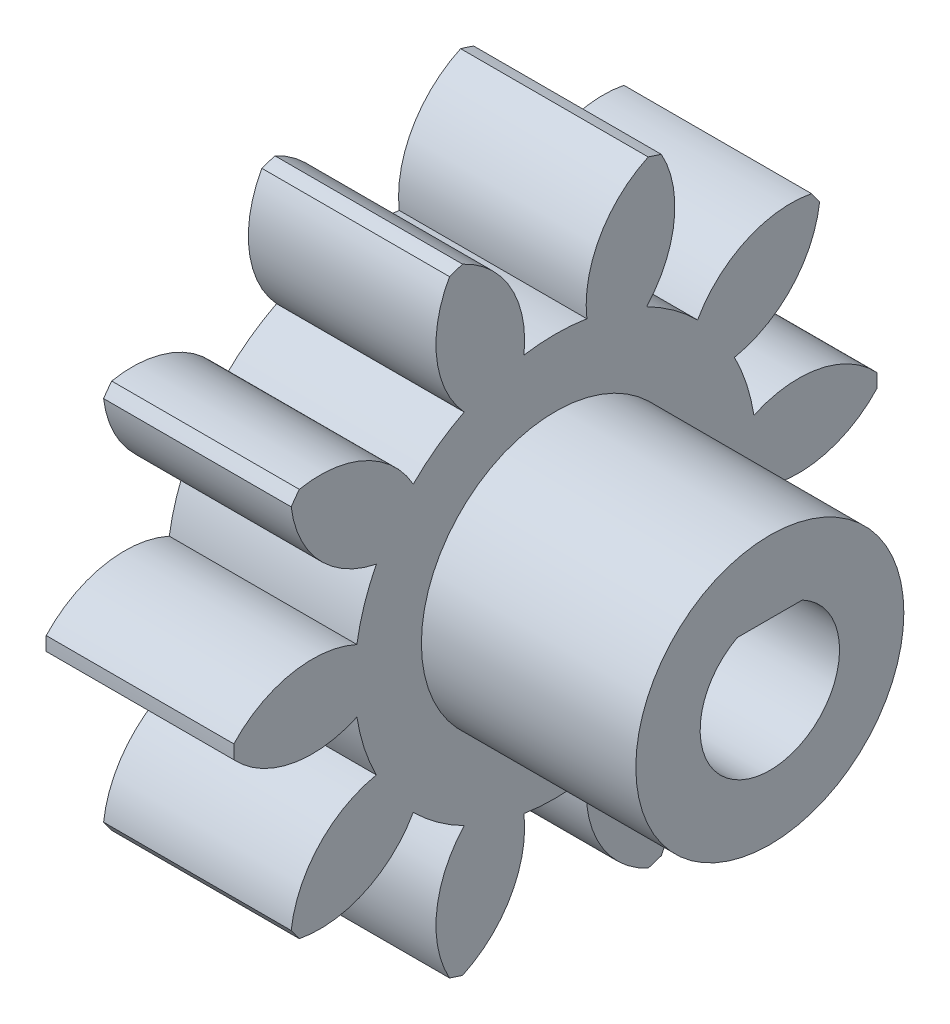
SolidWorks part; units mm, degrees
ref_plane "Plane1" through (0, 0, 0) normal (0, 0, 1) x (1, 0, 0)
ref_plane "Plane2" through (0, 0, 0) normal (0, 1, 0) x (1, 0, 0)
ref_plane "Plane3" through (0, 0, 0) normal (1, 0, 0) x (0, 0, -1)
other "Configuration Table"
sketch "HoldingSke" plane through (0, 0, 0) normal (0, 1, 0) x (1, 0, 0)
  line L0 (0, 0) -> (0.4924, -0.0868)
  line L1 (-15, 0) -> (100, 0) construction
  line L2 (0, 0) -> (-2.1039, 2.3779)
  line L3 (0, 0) -> (-11.863, 4.5341)
  line L4 (0, 0) -> (8.5048, 1.4996)
  line L5 (0, 0) -> (-46.8476, -17.4728)
  line L6 (0, 0) -> (-12.4344, -8.3896)
  line L7 (-2.1039, 2.3779) -> (8.6586, 51.2059)
  line L8 (-76.2, 54.61) -> (-76.1, 54.61)
  line L9 (-71.009, 38.7566) -> (-53.1078, 45.2721)
  line L10 (-76.2, 71.12) -> (104.1128, 71.12)
  line L11 (0, 0) -> (-15, 0)
  line L12 (-76.2, 101.6) -> (-76.133, 101.6)
  line L13 (24.9733, 27.94) -> (52.9518, 28.4284)
  line L14 (24.9733, 27.94) -> (24.9743, 27.94)
  line L15 (24.9733, 27.94) -> (100.4006, 29.5858)
  line L16 (-63.627, -2) -> (-12.827, -2)
  circle A0 centre (0, 0) radius 0.45
  circle A1 centre (0, 0) radius 7.499
  circle A2 centre (0, 0) radius 37.5
  circle A3 centre (0, 0) radius 0.45
  dimension "MHD" = 14.998
  dimension "Hub_dia" = 75
  dimension "Bore" = 0.9
  dimension "MBD" = 0.9
  dimension "Num_teeth" = 10
  dimension "Pitch" = 0.5
  dimension "Overall_len" = 50
  dimension "Show_teeth" = 10
  dimension "Thickness" = 15
  dimension "OAL" = 50.0001
  dimension "T_dim" = 0.1
  dimension "Ap" = 20
  dimension "H" = 19.05
  dimension "Pitch_radius" = 180.3128
  dimension "Width" = 15
  dimension "Backlash" = 0.067
  dimension "Addendum_fac" = 1
  dimension "Dedendum_fac" = 1.25
  dimension "Clearance_fac" = 0.25
  dimension "Dedendum_add" = 0.001
  dimension "Module" = 2
sketch "BasProSke" plane through (0, 0, 0) normal (0, 1, 0) x (1, 0, 0)
  line L0 (-10, 0) -> (60, 0) construction
  line L1 (0, 0) -> (0, 12)
  line L2 (0, 0) -> (15, 0)
  line L3 (15, 0) -> (15, 12)
  line L4 (15, 12) -> (0, 12)
  dimension "Thickness" = 15
  dimension "Diameter" = 24
revolve "Base-Revolve" add sketch "BasProSke" angle 360 about L0
sketch "TooCutSke" plane through (0, 0, 0) normal (1, 0, 0) x (0, 0, -1)
  line L1 (0, 0) -> (0, 107) construction
  line L2 (0, 0) -> (-1.6814, 9.8576) construction
  line L3 (0, 0) -> (-6.1153, 18.8209) construction
  line L4 (-1.6814, 9.8576) -> (-3.0576, 9.4105) construction
  arc A0 (1.1737, 7.4066) -> (-1.1737, 7.4066) centre (0, 0) ccw
  arc A1 (3.4979, 11.5054) -> (-3.4979, 11.5054) centre (0, 0) ccw
  circle A2 centre (0, 0) radius 10 construction
  circle A3 centre (0, 0) radius 9.3969 construction
  arc A4 (-1.1737, 7.4066) -> (-3.4979, 11.5054) centre (-5.1477, 7.8615) ccw
  arc A5 (3.4979, 11.5054) -> (1.1737, 7.4066) centre (5.1477, 7.8615) ccw
  dimension "Root_dia" = 14.998
  dimension "Overcut_dia" = 24.0508
  dimension "Pitch_dia" = 20
  dimension "Base_dia" = 18.7939
  dimension "Flank_rad" = 4
  dimension "Half_ang" = 18
  dimension "Half_CT" = 1.4471
extrude "ToothCut" cut sketch "TooCutSke" along normal through all
fillet "Breaks" [suppressed] radius 0.04
fillet "RootFillets" [suppressed] radius 0.501
pattern_circular "TeethCuts" count 10 every 36 about axis through (-10, 0, 0) along (1, 0, 0) of "ToothCut", "RootFillets", "Breaks"
sketch "HubNeaOneSke" plane through (0, 0, 0) normal (-1, 0, 0) x (0, 0, 1)
  circle A0 centre (0, 0) radius 7.499
  dimension "Diameter" = 14.998
extrude "HubNearOne" [suppressed] add sketch "HubNeaOneSke" along normal blind 35.0001
sketch "HubNeaBotSke" plane through (0, 0, 0) normal (-1, 0, 0) x (0, 0, 1)
  circle A0 centre (0, 0) radius 7.499
  dimension "Diameter" = 14.998
extrude "HubNearBoth" [suppressed] add sketch "HubNeaBotSke" along normal blind 17.5
ref_plane "FarPln" through (15, 0, 0) normal (1, 0, 0) x (0, 0, -1)
sketch "HubFarSke" plane through (15, 0, 0) normal (1, 0, 0) x (0, 0, -1)
  circle A0 centre (0, 0) radius 7.499
  dimension "Diameter" = 14.998
extrude "HubFar" [suppressed] add sketch "HubFarSke" along normal blind 17.5
sketch "BorSke" plane through (0, 0, 0) normal (1, 0, 0) x (0, 0, -1)
  circle A0 centre (0, 0) radius 0.45
  dimension "Diameter" = 0.9
extrude "Bore" cut sketch "BorSke" along normal mid plane 100.0001
sketch "KeySke" plane through (0, 0, 0) normal (1, 0, 0) x (0, 0, -1)
  line L0 (-0.05, 0) -> (-0.05, 0.55)
  line L1 (-0.05, 0.55) -> (0.05, 0.55)
  line L2 (0.05, 0.55) -> (0.05, 0)
  line L3 (0, 0) -> (0, 34) construction
  line L4 (-0.05, 0) -> (0.05, 0)
  dimension "Offset" = 0.55
  dimension "Width" = 0.1
extrude "Keyway" [suppressed] cut sketch "KeySke" along normal mid plane 100.0001
pattern_circular "Keyway2" [suppressed] count 2 every 90 about axis through (-10, 0, 0) along (1, 0, 0)
sketch "Sketch1" plane through (0, 0, 0) normal (-1, 0, 0) x (0, 0, 1)
  line L0 (0, 0) -> (0, 2.3) construction
  line L1 (-1.2124, 2.3) -> (1.2124, 2.3)
  circle A0 centre (0, 0) radius 2.6
  point P7 (0, 2.3)
extrude "Cut-Extrude1" cut sketch "Sketch1" against normal blind 15
sketch "Sketch5" plane through (0, 0, 0) normal (-1, 0, 0) x (0, 0, 1)
  arc A40 (-7.4068, 1.1725) -> (-11.9973, 0.2569) centre (-9.0675, -2.4664) ccw
  arc A41 (-11.9973, 0.2569) -> (-11.9973, -0.2569) centre (0, 0) ccw
  arc A42 (-11.9973, -0.2569) -> (-7.4068, -1.1725) centre (-9.0675, 2.4664) ccw
  arc A43 (-7.4068, -1.1725) -> (-6.6814, -3.405) centre (0, 0) ccw
  arc A44 (-6.6814, -3.405) -> (-9.857, -6.844) centre (-5.886, -7.3251) ccw
  arc A45 (-9.857, -6.844) -> (-9.555, -7.2596) centre (0, 0) ccw
  arc A46 (-9.555, -7.2596) -> (-5.303, -5.3022) centre (-8.7855, -3.3343) ccw
  arc A47 (-5.303, -5.3022) -> (-3.404, -6.6819) centre (0, 0) ccw
  arc A48 (-3.404, -6.6819) -> (-3.9517, -11.3307) centre (-0.4563, -9.3858) ccw
  arc A49 (-3.9517, -11.3307) -> (-3.463, -11.4894) centre (0, 0) ccw
  arc A50 (-3.463, -11.4894) -> (-1.1737, -7.4066) centre (-5.1477, -7.8615) ccw
  arc A51 (-1.1737, -7.4066) -> (1.1737, -7.4066) centre (0, 0) ccw
  arc A52 (1.1737, -7.4066) -> (3.463, -11.4894) centre (5.1477, -7.8615) ccw
  arc A53 (3.463, -11.4894) -> (3.9517, -11.3307) centre (0, 0) ccw
  arc A54 (3.9517, -11.3307) -> (3.404, -6.6819) centre (0.4563, -9.3858) ccw
  arc A55 (3.404, -6.6819) -> (5.303, -5.3022) centre (0, 0) ccw
  arc A56 (5.303, -5.3022) -> (9.555, -7.2596) centre (8.7855, -3.3343) ccw
  arc A57 (9.555, -7.2596) -> (9.857, -6.844) centre (0, 0) ccw
  arc A58 (9.857, -6.844) -> (6.6814, -3.405) centre (5.886, -7.3251) ccw
  arc A59 (6.6814, -3.405) -> (7.4068, -1.1725) centre (0, 0) ccw
  arc A60 (7.4068, -1.1725) -> (11.9973, -0.2569) centre (9.0675, 2.4664) ccw
  arc A61 (11.9973, -0.2569) -> (11.9973, 0.2569) centre (0, 0) ccw
  arc A62 (11.9973, 0.2569) -> (7.4068, 1.1725) centre (9.0675, -2.4664) ccw
  arc A63 (7.4068, 1.1725) -> (6.6814, 3.405) centre (0, 0) ccw
  arc A64 (6.6814, 3.405) -> (9.857, 6.844) centre (5.886, 7.3251) ccw
  arc A65 (9.857, 6.844) -> (9.555, 7.2596) centre (0, 0) ccw
  arc A66 (9.555, 7.2596) -> (5.303, 5.3022) centre (8.7855, 3.3343) ccw
  arc A67 (5.303, 5.3022) -> (3.404, 6.6819) centre (0, 0) ccw
  arc A68 (3.404, 6.6819) -> (3.9517, 11.3307) centre (0.4563, 9.3858) ccw
  arc A69 (3.9517, 11.3307) -> (3.463, 11.4894) centre (0, 0) ccw
  arc A70 (3.463, 11.4894) -> (1.1737, 7.4066) centre (5.1477, 7.8615) ccw
  arc A71 (1.1737, 7.4066) -> (-1.1737, 7.4066) centre (0, 0) ccw
  arc A72 (-1.1737, 7.4066) -> (-3.463, 11.4894) centre (-5.1477, 7.8615) ccw
  arc A73 (-3.463, 11.4894) -> (-3.9517, 11.3307) centre (0, 0) ccw
  arc A74 (-3.9517, 11.3307) -> (-3.404, 6.6819) centre (-0.4563, 9.3858) ccw
  arc A75 (-3.404, 6.6819) -> (-5.303, 5.3022) centre (0, 0) ccw
  arc A76 (-5.303, 5.3022) -> (-9.555, 7.2596) centre (-8.7855, 3.3343) ccw
  arc A77 (-9.555, 7.2596) -> (-9.857, 6.844) centre (0, 0) ccw
  arc A78 (-9.857, 6.844) -> (-6.6814, 3.405) centre (-5.886, 7.3251) ccw
  arc A79 (-6.6814, 3.405) -> (-7.4068, 1.1725) centre (0, 0) ccw
  arc A80 (-7.4068, 1.1725) -> (-11.9973, 0.2569) centre (-9.0675, -2.4664) ccw
  arc A81 (-11.9973, 0.2569) -> (-11.9973, -0.2569) centre (0, 0) ccw
  arc A82 (-11.9973, -0.2569) -> (-7.4068, -1.1725) centre (-9.0675, 2.4664) ccw
  arc A83 (-7.4068, -1.1725) -> (-6.6814, -3.405) centre (0, 0) ccw
  arc A84 (-6.6814, -3.405) -> (-9.857, -6.844) centre (-5.886, -7.3251) ccw
  arc A85 (-9.857, -6.844) -> (-9.555, -7.2596) centre (0, 0) ccw
  arc A86 (-9.555, -7.2596) -> (-5.303, -5.3022) centre (-8.7855, -3.3343) ccw
  arc A87 (-5.303, -5.3022) -> (-3.404, -6.6819) centre (0, 0) ccw
  arc A88 (-3.404, -6.6819) -> (-3.9517, -11.3307) centre (-0.4563, -9.3858) ccw
  arc A89 (-3.9517, -11.3307) -> (-3.463, -11.4894) centre (0, 0) ccw
  arc A90 (-3.463, -11.4894) -> (-1.1737, -7.4066) centre (-5.1477, -7.8615) ccw
  arc A91 (-1.1737, -7.4066) -> (1.1737, -7.4066) centre (0, 0) ccw
  arc A92 (1.1737, -7.4066) -> (3.463, -11.4894) centre (5.1477, -7.8615) ccw
  arc A93 (3.463, -11.4894) -> (3.9517, -11.3307) centre (0, 0) ccw
  arc A94 (3.9517, -11.3307) -> (3.404, -6.6819) centre (0.4563, -9.3858) ccw
  arc A95 (3.404, -6.6819) -> (5.303, -5.3022) centre (0, 0) ccw
  arc A96 (5.303, -5.3022) -> (9.555, -7.2596) centre (8.7855, -3.3343) ccw
  arc A97 (9.555, -7.2596) -> (9.857, -6.844) centre (0, 0) ccw
  arc A98 (9.857, -6.844) -> (6.6814, -3.405) centre (5.886, -7.3251) ccw
  arc A99 (6.6814, -3.405) -> (7.4068, -1.1725) centre (0, 0) ccw
  arc A100 (7.4068, -1.1725) -> (11.9973, -0.2569) centre (9.0675, 2.4664) ccw
  arc A101 (11.9973, -0.2569) -> (11.9973, 0.2569) centre (0, 0) ccw
  arc A102 (11.9973, 0.2569) -> (7.4068, 1.1725) centre (9.0675, -2.4664) ccw
  arc A103 (7.4068, 1.1725) -> (6.6814, 3.405) centre (0, 0) ccw
  arc A104 (6.6814, 3.405) -> (9.857, 6.844) centre (5.886, 7.3251) ccw
  arc A105 (9.857, 6.844) -> (9.555, 7.2596) centre (0, 0) ccw
  arc A106 (9.555, 7.2596) -> (5.303, 5.3022) centre (8.7855, 3.3343) ccw
  arc A107 (5.303, 5.3022) -> (3.404, 6.6819) centre (0, 0) ccw
  arc A108 (3.404, 6.6819) -> (3.9517, 11.3307) centre (0.4563, 9.3858) ccw
  arc A109 (3.9517, 11.3307) -> (3.463, 11.4894) centre (0, 0) ccw
  arc A110 (3.463, 11.4894) -> (1.1737, 7.4066) centre (5.1477, 7.8615) ccw
  arc A111 (1.1737, 7.4066) -> (-1.1737, 7.4066) centre (0, 0) ccw
  arc A112 (-1.1737, 7.4066) -> (-3.463, 11.4894) centre (-5.1477, 7.8615) ccw
  arc A113 (-3.463, 11.4894) -> (-3.9517, 11.3307) centre (0, 0) ccw
  arc A114 (-3.9517, 11.3307) -> (-3.404, 6.6819) centre (-0.4563, 9.3858) ccw
  arc A115 (-3.404, 6.6819) -> (-5.303, 5.3022) centre (0, 0) ccw
  arc A116 (-5.303, 5.3022) -> (-9.555, 7.2596) centre (-8.7855, 3.3343) ccw
  arc A117 (-9.555, 7.2596) -> (-9.857, 6.844) centre (0, 0) ccw
  arc A118 (-9.857, 6.844) -> (-6.6814, 3.405) centre (-5.886, 7.3251) ccw
  arc A119 (-6.6814, 3.405) -> (-7.4068, 1.1725) centre (0, 0) ccw
  dimension "D1" = 0
extrude "Cut-Extrude2" cut sketch "Sketch5" against normal blind 8
sketch "Sketch6" plane through (15, 0, 0) normal (1, 0, 0) x (0, 0, -1)
  line L0 (1.2124, 2.3) -> (-1.2124, 2.3) construction
  line L1 (1.2124, 2.3) -> (-1.2124, 2.3)
  circle A0 centre (0, 0) radius 5
  arc A1 (-1.2124, 2.3) -> (1.2124, 2.3) centre (0, 0) ccw construction
  arc A2 (-1.2124, 2.3) -> (1.2124, 2.3) centre (0, 0) ccw
extrude "Boss-Extrude1" add sketch "Sketch6" along normal blind 8
equation "' \"Module@HoldingSke\" = 6.35"
equation "' \"Num_teeth@HoldingSke\" = 12"
equation "' \"Ap@HoldingSke\" =  20"
equation "' \"Ap@HoldingSke\" = 20"
equation "' \"Width@HoldingSke\" = 0.5 * 25.4"
equation "' \"Hub_dia@HoldingSke\"= 1 * 25.4"
equation "' \"Hub_dia@HoldingSke\" = 1 * 25.4"
equation "' \"Overall_len@HoldingSke\" = 1.0 * 25.4"
equation "' \"Bore@HoldingSke\" = 0.75 * 25.4"
equation "' \"T_dim@HoldingSke\" = 0.1 * 25.4"
equation "' \"Width@KeySke\" = 0.25 * 25.4"
equation "' \"Show_teeth@HoldingSke\" = 13"
equation "' \"Backlash@HoldingSke\" = 0.009 * 25.4"
equation "' \"Addendum_fac@HoldingSke\" = 1.0"
equation "' \"Dedendum_fac@HoldingSke\" = 1.25"
equation "' \"Dedendum_add@HoldingSke\" = 0.00005 * 25.4"
equation "' \"Clearance_fac@HoldingSke\" = 0.25"
equation "\"Pitch@HoldingSke\" = 1 / \"Module@HoldingSke\""
equation "\"Overcut_dia@TooCutSke\" = (\"Num_teeth@HoldingSke\" + 2 * \"Addendum_fac@HoldingSke\") / \"Pitch@HoldingSke\" + 0.002 * 25.4"
equation "\"Pitch_dia@TooCutSke\" = \"Num_teeth@HoldingSke\" / \"Pitch@HoldingSke\""
equation "\"Base_dia@TooCutSke\" = \"Num_teeth@HoldingSke\" / \"Pitch@HoldingSke\" * cos((\"Ap@HoldingSke\"  * 3.14159265 / 180))"
equation "\"Root_dia@TooCutSke\" = (\"Num_teeth@HoldingSke\" + 2) / \"Pitch@HoldingSke\" - 2 * (\"Addendum_fac@HoldingSke\" + \"Dedendum_fac@HoldingSke\") / \"Pitch@HoldingSke\" - \"Dedendum_add@HoldingSke\" * 2"
equation "\"Half_ang@TooCutSke\" = 180 / \"Num_teeth@HoldingSke\""
equation "\"Half_CT@TooCutSke\" = \"Num_teeth@HoldingSke\" / \"Pitch@HoldingSke\" * sin((3.14159265 / 2 / \"Num_teeth@HoldingSke\")) / 2 - 7 * \"Backlash@HoldingSke\" / 4"
equation "\"Flank_rad@TooCutSke\" = \"Num_teeth@HoldingSke\" / \"Pitch@HoldingSke\" / 5"
equation "\"Radius@RootFillets\" = \"Clearance_fac@HoldingSke\" / \"Pitch@HoldingSke\" + \"Dedendum_add@HoldingSke\""
equation "\"Break_rad@Breaks\" = 0.02 / \"Pitch@HoldingSke\""
equation "\"Thickness@HoldingSke\" = \"Width@HoldingSke\""
equation "\"OAL@HoldingSke\" = \"Thickness@HoldingSke\""
equation "\"MHD@HoldingSke\" = (\"Num_teeth@HoldingSke\" + 2) / \"Pitch@HoldingSke\" - 2 * (\"Addendum_fac@HoldingSke\" + \"Dedendum_fac@HoldingSke\")  / \"Pitch@HoldingSke\" - \"Dedendum_add@HoldingSke\" * 2"
equation "\"MBD@HoldingSke\" = (\"Num_teeth@HoldingSke\" + 2) / \"Pitch@HoldingSke\" - 2 * (\"Addendum_fac@HoldingSke\" + \"Dedendum_fac@HoldingSke\")  / \"Pitch@HoldingSke\" - \"Dedendum_add@HoldingSke\" * 2 - 0.002 * 25.4"
equation "\"MHD@HoldingSke\" = ((sgn( \"MHD@HoldingSke\" - \"Hub_dia@HoldingSke\" )-1)*( \"MHD@HoldingSke\" - \"Hub_dia@HoldingSke\" ))/-2+ \"Hub_dia@HoldingSke\""
equation "\"MBD@HoldingSke\" = ((sgn( \"MBD@HoldingSke\" - \"Bore@HoldingSke\" )-1)*( \"MBD@HoldingSke\" - \"Bore@HoldingSke\" ))/-2+ \"Bore@HoldingSke\""
equation "\"OAL@HoldingSke\" = ((sgn( \"OAL@HoldingSke\" - \"Overall_len@HoldingSke\" )+1)*( \"OAL@HoldingSke\" - \"Overall_len@HoldingSke\" ))/2 + \"Overall_len@HoldingSke\" + 0.000002 * 25.4"
equation "\"Num_teeth@TeethCuts\" = int( \"Show_teeth@HoldingSke\" ) + 1"
equation "\"Num_teeth@TeethCuts\" = ((sgn( \"Num_teeth@TeethCuts\" - \"Num_teeth@HoldingSke\" )-1)*( \"Num_teeth@TeethCuts\" - \"Num_teeth@HoldingSke\" ))/-2+ \"Num_teeth@HoldingSke\""
equation "\"Num_teeth@TeethCuts\" = ((sgn( \"Num_teeth@TeethCuts\" - 2.0)+1)*( \"Num_teeth@TeethCuts\" - 2.0))/2 +2.0"
equation "\"Angle@TeethCuts\" = 360.0 / \"Num_teeth@HoldingSke\""
equation "\"Diameter@BasProSke\" = (\"Num_teeth@HoldingSke\" + 2 * \"Addendum_fac@HoldingSke\") / \"Pitch@HoldingSke\""
equation "\"Thickness@BasProSke\"  = \"Thickness@HoldingSke\""
equation "' \"Fillet_rad@BasProSke\" =  \"Thickness@HoldingSke\" * 0.05"
equation "' \"Fillet_rad@BasProSke\" = \"Thickness@HoldingSke\" * 0.05"
equation "\"MHD@HoldingSke\" = ((sgn( \"MHD@HoldingSke\" - \"Root_dia@TooCutSke\" )-1)*( \"MHD@HoldingSke\" - \"Root_dia@TooCutSke\" ))/-2+ \"Root_dia@TooCutSke\""
equation "\"Diameter@HubNeaOneSke\" = \"MHD@HoldingSke\""
equation "\"Length@HubNearOne\" = \"OAL@HoldingSke\" - \"Thickness@BasProSke\""
equation "\"Diameter@HubNeaBotSke\" = \"MHD@HoldingSke\""
equation "\"Length@HubNearBoth\" = ( \"OAL@HoldingSke\" - \"Thickness@BasProSke\" ) / 2.0"
equation "\"Thickness@FarPln\" = \"Thickness@BasProSke\""
equation "\"Diameter@HubFarSke\" = \"MHD@HoldingSke\""
equation "\"Length@HubFar\" = ( \"OAL@HoldingSke\" - \"Thickness@BasProSke\" ) / 2.0"
equation "\"Diameter@BorSke\" = \"MBD@HoldingSke\""
equation "\"D1@Bore\" = \"OAL@HoldingSke\" * 2.0"
equation "\"D1@Keyway\" = \"OAL@HoldingSke\" * 2.0"
equation "\"Offset@KeySke\" = \"T_dim@HoldingSke\" + \"MBD@HoldingSke\" / 2.0"
